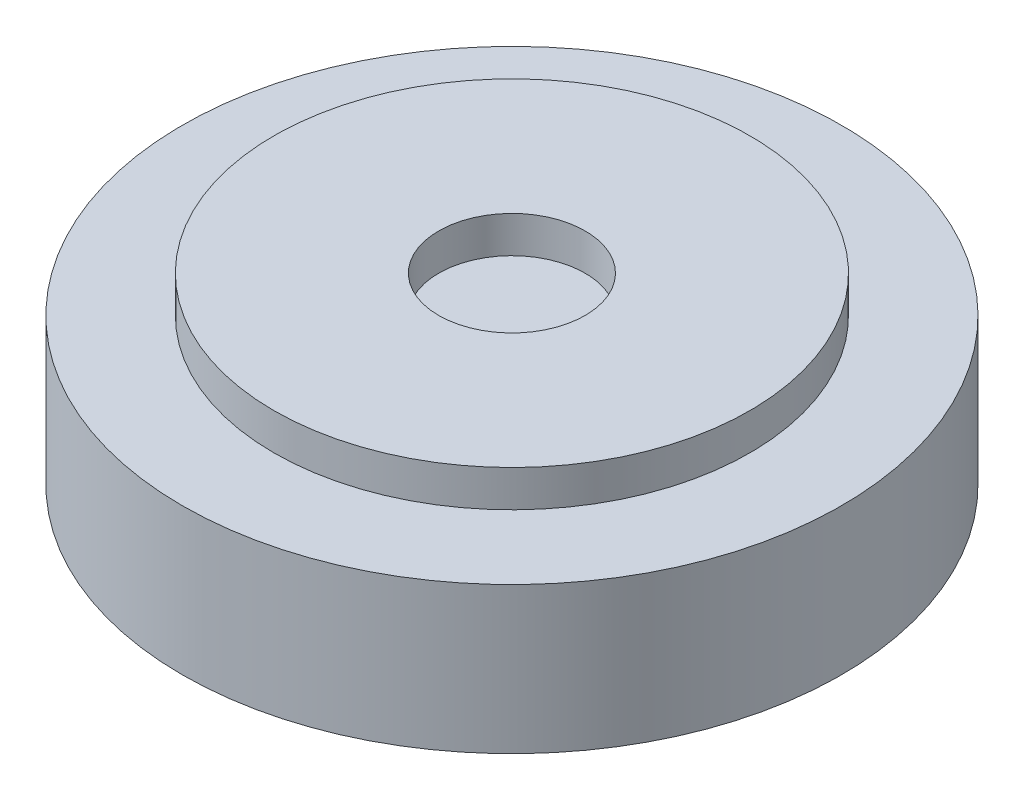
SolidWorks part; units mm, degrees
ref_plane "前视基准面" through (0, 0, 0) normal (0, 0, 1) x (1, 0, 0)
ref_plane "上视基准面" through (0, 0, 0) normal (0, 1, 0) x (1, 0, 0)
ref_plane "右视基准面" through (0, 0, 0) normal (1, 0, 0) x (0, 0, -1)
sketch "草图1" plane through (0, 0, 0) normal (0, 1, 0) x (1, 0, 0)
  circle A0 centre (0, 0) radius 9
  dimension "D1" = 18
extrude "凸台-拉伸1" add sketch "草图1" along normal blind 5
sketch "草图2" plane through (0, 5, 0) normal (0, 1, 0) x (1, 0, 0)
  circle A0 centre (0, 0) radius 6.5
extrude "切除-拉伸1" cut sketch "草图2" against normal blind 1 flip side to cut
sketch "草图3" plane through (0, 5, 0) normal (0, 1, 0) x (1, 0, 0)
  circle A0 centre (0, 0) radius 2
extrude "切除-拉伸2" cut sketch "草图3" against normal blind 1
